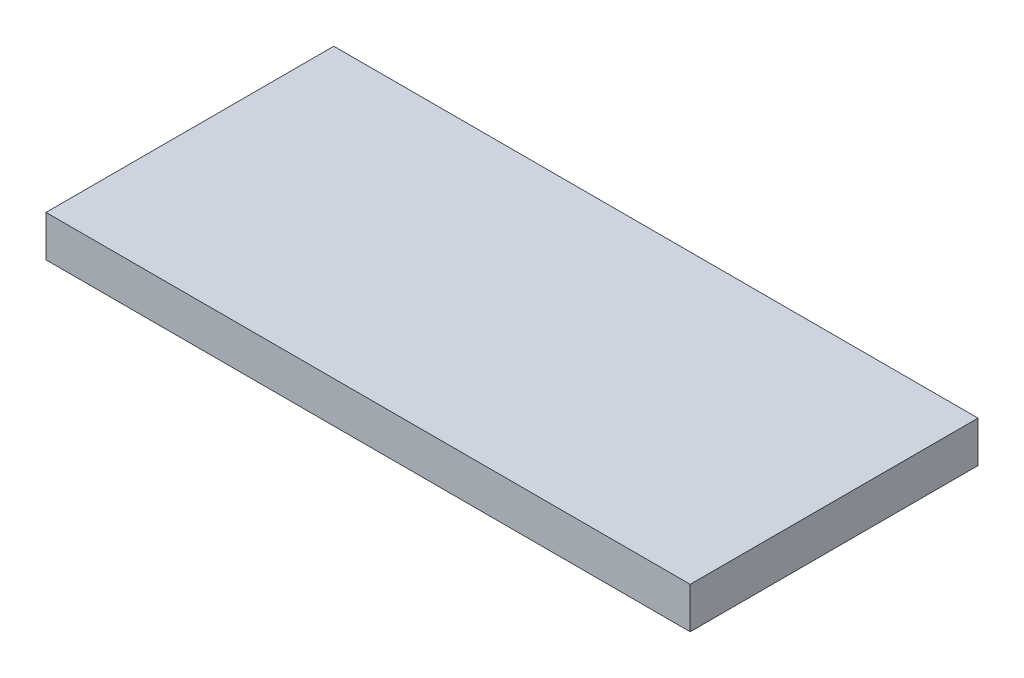
SolidWorks part; units mm, degrees
ref_plane "Front Plane" through (0, 0, 0) normal (0, 0, 1) x (1, 0, 0)
ref_plane "Top Plane" through (0, 0, 0) normal (0, 1, 0) x (1, 0, 0)
ref_plane "Right Plane" through (0, 0, 0) normal (1, 0, 0) x (0, 0, -1)
sketch "Sketch1" plane through (0, 0, 0) normal (0, 1, 0) x (1, 0, 0)
  line L1 (-47, 21) -> (47, 21)
  line L2 (-47, 21) -> (-47, -21)
  line L3 (-47, -21) -> (47, -21)
  line L4 (47, 21) -> (47, -21)
  line L5 (-47, 21) -> (47, -21) construction
  line L6 (-47, -21) -> (47, 21) construction
  point P0 (0, 0)
  dimension "D1" = 94
  dimension "D2" = 42
sketch "Sketch2" plane through (0, 0, 0) normal (0, 0, 1) x (1, 0, 0)
  line L0 (0, 0) -> (0, 6) construction
  line L1 (-47, 0) -> (47, 0) construction
  dimension "D1" = 6
extrude "Boss-Extrude1" add sketch "Sketch1" along normal up to vertex (6 mm away) contours L2 L3 L4 L1 up to point (0, 6, 0)
equation "\"glass_width\" = 150"
equation "\"glass_height\"= 100"
equation "\"glass_thickness\"= 4"
equation "\"brood_space\"= 42"
equation "\"t1\"= 6"
equation "\"t2\"= 3.2"
equation "\"box_depth\"= \"brood_space\" + \"glass_thickness\" + \"glass_thickness\" + \"t2\" + \"t2\""
equation "\"box_width\"= \"glass_width\" + \"t1\" + \"t1\""
equation "\"food_height\"= 70"
equation "\"box_height\" = \"glass_height\" + ( \"t1\" * 3 ) + \"food_height\""
equation "\"D1@Sketch2\"=\"t1\""
equation "\"D1@Sketch1\"=\"glass_height\" - \"t1\""
equation "\"D2@Sketch1\"=\"brood_space\""
